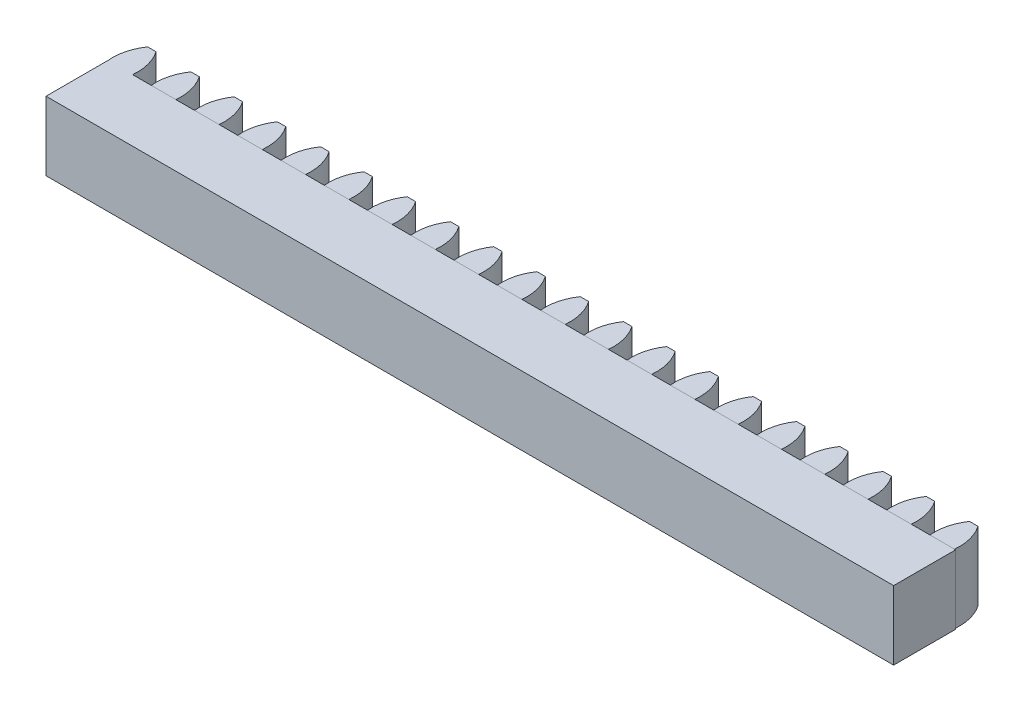
SolidWorks part; units mm, degrees
ref_plane "前视基准面" through (0, 0, 0) normal (0, 0, 1) x (1, 0, 0)
ref_plane "上视基准面" through (0, 0, 0) normal (0, 1, 0) x (1, 0, 0)
ref_plane "右视基准面" through (0, 0, 0) normal (1, 0, 0) x (0, 0, -1)
sketch "草图1" plane through (0, 0, 0) normal (0, 1, 0) x (1, 0, 0)
  line L4 (0, 0) -> (3.5684, 0)
  line L81 (1.174, 4.582) -> (2.3945, 4.582)
  line L82 (1.7842, 4.582) -> (1.7842, 0) construction
  line L83 (6.28, 0) -> (9.8484, 0)
  line L84 (7.454, 4.582) -> (8.6745, 4.582)
  line L85 (12.56, 0) -> (16.1284, 0)
  line L86 (13.734, 4.582) -> (14.9545, 4.582)
  line L87 (18.84, 0) -> (22.4084, 0)
  line L88 (20.014, 4.582) -> (21.2345, 4.582)
  line L89 (25.12, 0) -> (28.6884, 0)
  line L90 (26.294, 4.582) -> (27.5145, 4.582)
  line L91 (31.4, 0) -> (34.9684, 0)
  line L92 (32.574, 4.582) -> (33.7945, 4.582)
  line L93 (37.68, 0) -> (41.2484, 0)
  line L94 (38.854, 4.582) -> (40.0745, 4.582)
  line L95 (43.96, 0) -> (47.5284, 0)
  line L96 (45.134, 4.582) -> (46.3545, 4.582)
  line L97 (50.24, 0) -> (53.8084, 0)
  line L98 (51.414, 4.582) -> (52.6345, 4.582)
  line L99 (56.52, 0) -> (60.0884, 0)
  line L100 (57.694, 4.582) -> (58.9145, 4.582)
  line L101 (62.8, 0) -> (66.3684, 0)
  line L102 (63.974, 4.582) -> (65.1945, 4.582)
  line L103 (69.08, 0) -> (72.6484, 0)
  line L104 (70.254, 4.582) -> (71.4745, 4.582)
  line L105 (75.36, 0) -> (78.9284, 0)
  line L106 (76.534, 4.582) -> (77.7545, 4.582)
  line L107 (81.64, 0) -> (85.2084, 0)
  line L108 (82.814, 4.582) -> (84.0345, 4.582)
  line L109 (87.92, 0) -> (91.4884, 0)
  line L110 (89.094, 4.582) -> (90.3145, 4.582)
  line L111 (94.2, 0) -> (97.7684, 0)
  line L112 (95.374, 4.582) -> (96.5945, 4.582)
  line L113 (100.48, 0) -> (104.0484, 0)
  line L114 (101.654, 4.582) -> (102.8745, 4.582)
  line L115 (106.76, 0) -> (110.3284, 0)
  line L116 (107.934, 4.582) -> (109.1545, 4.582)
  line L117 (113.04, 0) -> (116.6084, 0)
  line L118 (114.214, 4.582) -> (115.4345, 4.582)
  line L119 (119.32, 0) -> (122.8884, 0)
  line L120 (120.494, 4.582) -> (121.7145, 4.582)
  arc A0 (0, 0) -> (1.174, 4.582) centre (6.8047, 0.698) cw
  arc A1 (3.5684, 0) -> (2.3945, 4.582) centre (-3.2363, 0.698) ccw
  arc A2 (9.8484, 0) -> (8.6745, 4.582) centre (3.0437, 0.698) ccw
  arc A3 (6.28, 0) -> (7.454, 4.582) centre (13.0847, 0.698) cw
  arc A4 (16.1284, 0) -> (14.9545, 4.582) centre (9.3237, 0.698) ccw
  arc A5 (12.56, 0) -> (13.734, 4.582) centre (19.3647, 0.698) cw
  arc A6 (22.4084, 0) -> (21.2345, 4.582) centre (15.6037, 0.698) ccw
  arc A7 (18.84, 0) -> (20.014, 4.582) centre (25.6447, 0.698) cw
  arc A8 (28.6884, 0) -> (27.5145, 4.582) centre (21.8837, 0.698) ccw
  arc A9 (25.12, 0) -> (26.294, 4.582) centre (31.9247, 0.698) cw
  arc A10 (34.9684, 0) -> (33.7945, 4.582) centre (28.1637, 0.698) ccw
  arc A11 (31.4, 0) -> (32.574, 4.582) centre (38.2047, 0.698) cw
  arc A12 (41.2484, 0) -> (40.0745, 4.582) centre (34.4437, 0.698) ccw
  arc A13 (37.68, 0) -> (38.854, 4.582) centre (44.4847, 0.698) cw
  arc A14 (47.5284, 0) -> (46.3545, 4.582) centre (40.7237, 0.698) ccw
  arc A15 (43.96, 0) -> (45.134, 4.582) centre (50.7647, 0.698) cw
  arc A16 (53.8084, 0) -> (52.6345, 4.582) centre (47.0037, 0.698) ccw
  arc A17 (50.24, 0) -> (51.414, 4.582) centre (57.0447, 0.698) cw
  arc A18 (60.0884, 0) -> (58.9145, 4.582) centre (53.2837, 0.698) ccw
  arc A19 (56.52, 0) -> (57.694, 4.582) centre (63.3247, 0.698) cw
  arc A20 (66.3684, 0) -> (65.1945, 4.582) centre (59.5637, 0.698) ccw
  arc A21 (62.8, 0) -> (63.974, 4.582) centre (69.6047, 0.698) cw
  arc A22 (72.6484, 0) -> (71.4745, 4.582) centre (65.8437, 0.698) ccw
  arc A23 (69.08, 0) -> (70.254, 4.582) centre (75.8847, 0.698) cw
  arc A24 (78.9284, 0) -> (77.7545, 4.582) centre (72.1237, 0.698) ccw
  arc A25 (75.36, 0) -> (76.534, 4.582) centre (82.1647, 0.698) cw
  arc A26 (85.2084, 0) -> (84.0345, 4.582) centre (78.4037, 0.698) ccw
  arc A27 (81.64, 0) -> (82.814, 4.582) centre (88.4447, 0.698) cw
  arc A28 (91.4884, 0) -> (90.3145, 4.582) centre (84.6837, 0.698) ccw
  arc A29 (87.92, 0) -> (89.094, 4.582) centre (94.7247, 0.698) cw
  arc A30 (97.7684, 0) -> (96.5945, 4.582) centre (90.9637, 0.698) ccw
  arc A31 (94.2, 0) -> (95.374, 4.582) centre (101.0047, 0.698) cw
  arc A32 (104.0484, 0) -> (102.8745, 4.582) centre (97.2437, 0.698) ccw
  arc A33 (100.48, 0) -> (101.654, 4.582) centre (107.2847, 0.698) cw
  arc A34 (110.3284, 0) -> (109.1545, 4.582) centre (103.5237, 0.698) ccw
  arc A35 (106.76, 0) -> (107.934, 4.582) centre (113.5647, 0.698) cw
  arc A36 (116.6084, 0) -> (115.4345, 4.582) centre (109.8037, 0.698) ccw
  arc A37 (113.04, 0) -> (114.214, 4.582) centre (119.8447, 0.698) cw
  arc A38 (122.8884, 0) -> (121.7145, 4.582) centre (116.0837, 0.698) ccw
  arc A39 (119.32, 0) -> (120.494, 4.582) centre (126.1247, 0.698) cw
  point P5 (1.7842, 4.582)
  dimension "D1" = 6.8404
  dimension "D2" = 4.73
  dimension "D3" = 4.582
  dimension "D4" = 1.2205
extrude "凸台-拉伸1" add sketch "草图1" along normal blind 10
sketch "草图2" plane through (0, 10, 0) normal (0, 1, 0) x (1, 0, 0)
  line L5 (0, 0) -> (123.0494, 0)
  line L7 (0, 0) -> (0, -9)
  line L8 (0, -9) -> (123.0494, -9)
  line L9 (123.0494, 0) -> (123.0494, -9)
  dimension "D1" = 9
extrude "凸台-拉伸2" add sketch "草图2" against normal blind 10
